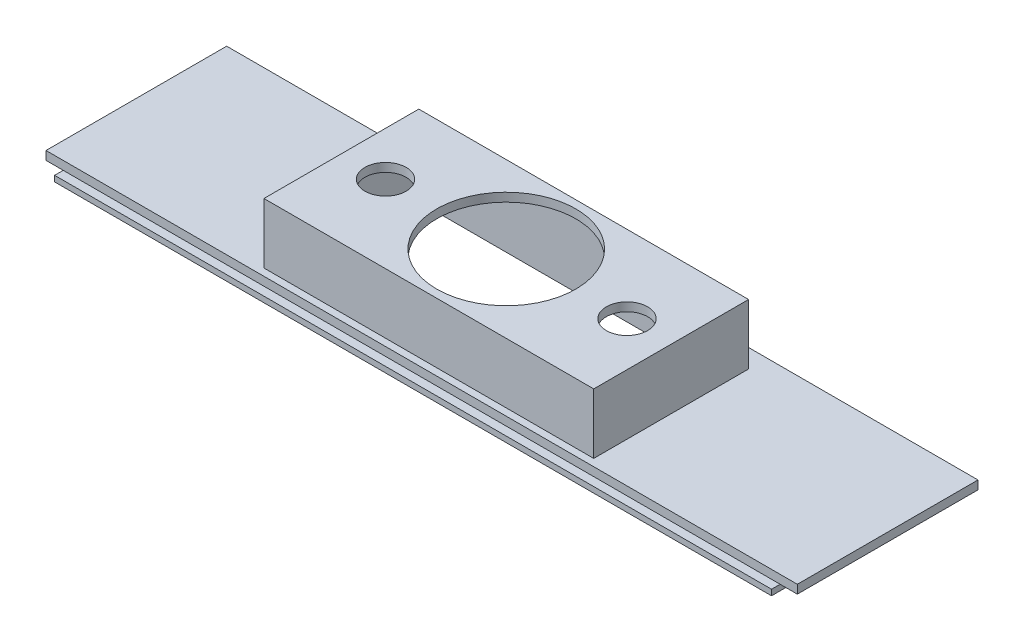
SolidWorks part; units mm, degrees
material "ABS"
ref_plane "Front Plane" through (0, 0, 0) normal (0, 0, 1) x (1, 0, 0)
ref_plane "Top Plane" through (0, 0, 0) normal (0, 1, 0) x (1, 0, 0)
ref_plane "Right Plane" through (0, 0, 0) normal (1, 0, 0) x (0, 0, -1)
sketch "Sketch1" plane through (0, 0, 0) normal (0, 1, 0) x (1, 0, 0)
  line L1 (-127, 29.5) -> (127, 29.5)
  line L2 (-127, 29.5) -> (-127, -29.5)
  line L3 (-127, -29.5) -> (127, -29.5)
  line L4 (127, 29.5) -> (127, -29.5)
  line L5 (0, -29.5) -> (0, 29.5) construction
  line L6 (-127, 0) -> (127, 0) construction
  point P0 (0, 0)
  dimension "D1" = 254
  dimension "D2" = 59
extrude "Boss-Extrude1" add sketch "Sketch1" along normal blind 3
sketch "Sketch2" plane through (0, 3, 0) normal (0, 1, 0) x (1, 0, 0)
  line L1 (-57.5, 27) -> (57.5, 27)
  line L2 (-57.5, 27) -> (-57.5, -27)
  line L3 (-57.5, -27) -> (57.5, -27)
  line L4 (57.5, 27) -> (57.5, -27)
  line L5 (0, -27) -> (0, 27) construction
  line L6 (-57.5, 0) -> (57.5, 0) construction
  line L10 (127, 29.5) -> (-127, 29.5) construction
  point P0 (0, 0)
  dimension "D1" = 115
  dimension "D2" = 54
extrude "Boss-Extrude2" add sketch "Sketch2" along normal blind 21
sketch "Sketch3" plane through (0, 0, 0) normal (0, -1, 0) x (1, 0, 0)
  line L0 (57.5, 27) -> (57.5, -27) construction
  line L1 (-57.5, -27) -> (-57.5, 27) construction
  line L2 (-57.5, 27) -> (57.5, 27) construction
  line L3 (57.5, 27) -> (57.5, -27)
  line L4 (-57.5, -27) -> (-57.5, 27)
  line L5 (-57.5, 27) -> (57.5, 27)
  line L6 (-57.5, -27) -> (57.5, -27)
  line L7 (-55.5, -25) -> (-55.5, 25)
  line L8 (-55.5, 25) -> (55.5, 25)
  line L9 (55.5, 25) -> (55.5, -25)
  line L10 (-55.5, -25) -> (55.5, -25)
  dimension "D1" = 2
extrude "Cut-Extrude3" cut sketch "Sketch3" against normal blind 21 contours L7 L10 L9 L8
sketch "Sketch4" plane through (0, 24, 0) normal (0, 1, 0) x (1, 0, 0)
  line L0 (-57.5, -27) -> (57.5, -27) construction
  line L1 (57.5, -27) -> (57.5, 27) construction
  line L2 (57.5, 27) -> (-57.5, 27) construction
  line L3 (-57.5, 27) -> (-57.5, -27) construction
  line L4 (-57.5, -27) -> (57.5, -27)
  line L5 (57.5, -27) -> (57.5, 27)
  line L6 (57.5, 27) -> (-57.5, 27)
  line L7 (-57.5, 27) -> (-57.5, -27)
  line L8 (-57.5, -27) -> (57.5, 27) construction
  line L9 (-57.5, 27) -> (57.5, -27) construction
  circle A0 centre (0, 0) radius 24.25
  circle A1 centre (-42.1, 0) radius 7.2
  circle A2 centre (42.1, 0) radius 7.2
  point P2 (0, 0)
  dimension "D1" = 48.5
  dimension "D2" = 14.4
  dimension "D3" = 42.1
  dimension "D4" = 42.1
extrude "Cut-Extrude4" cut sketch "Sketch4" against normal blind 3 contours A1 | A0 | A2
sketch "Sketch5" plane through (0, 0, 0) normal (0, -1, 0) x (1, 0, 0)
  line L0 (-125, -27.5) -> (125, -27.5)
  line L1 (125, -27.5) -> (125, 31.5)
  line L2 (125, 31.5) -> (-125, 31.5)
  line L3 (-125, 31.5) -> (-125, -27.5)
  line L4 (-127, -29.5) -> (-127, 29.5) construction
  line L5 (127, -29.5) -> (-127, -29.5) construction
  line L7 (127, 29.5) -> (127, -29.5) construction
  line L8 (-55.5, -25) -> (-55.5, 25) construction
  line L9 (-55.5, -25) -> (55.5, -25) construction
  line L10 (55.5, 25) -> (55.5, -25) construction
  line L11 (-55.5, 25) -> (55.5, 25) construction
  line L12 (-55.5, -25) -> (-55.5, 25)
  line L13 (-55.5, -25) -> (55.5, -25)
  line L14 (55.5, 25) -> (55.5, -25)
  line L15 (-55.5, 25) -> (55.5, 25)
  line L16 (-127, 29.5) -> (127, 29.5) construction
  dimension "D1" = 2
  dimension "D2" = 2
  dimension "D3" = 2
  dimension "D4" = 2
extrude "Boss-Extrude3" add sketch "Sketch5" along normal blind 2
sketch "Sketch6" plane through (-127, 0, 0) normal (-1, 0, 0) x (0, 0, 1)
  line L1 (-29.5, 3) -> (29.5, 3)
  line L2 (-29.5, 3) -> (-29.5, 0)
  line L3 (-29.5, 0) -> (29.5, 0)
  line L4 (29.5, 3) -> (29.5, 0)
extrude "Boss-Extrude4" add sketch "Sketch6" along normal blind 4
sketch "Sketch7" plane through (0, 0, -29.5) normal (0, 0, -1) x (-1, 0, 0)
  line L1 (-127, 3) -> (131, 3)
  line L2 (-127, 3) -> (-127, 0)
  line L3 (-127, 0) -> (131, 0)
  line L4 (131, 3) -> (131, 0)
extrude "Boss-Extrude5" add sketch "Sketch7" along normal blind 4
sketch "Sketch8" plane through (127, 0, 0) normal (1, 0, 0) x (0, 0, -1)
  line L1 (-29.5, 3) -> (33.5, 3)
  line L2 (-29.5, 3) -> (-29.5, 0)
  line L3 (-29.5, 0) -> (33.5, 0)
  line L4 (33.5, 3) -> (33.5, 0)
extrude "Boss-Extrude6" add sketch "Sketch8" along normal blind 4
sketch "Sketch9" plane through (0, 0, 31.5) normal (0, 0, 1) x (1, 0, 0)
  line L1 (-125, -2) -> (125, -2)
  line L2 (-125, -2) -> (-125, 0)
  line L3 (-125, 0) -> (125, 0)
  line L4 (125, -2) -> (125, 0)
extrude "Boss-Extrude7" add sketch "Sketch9" along normal blind 1
